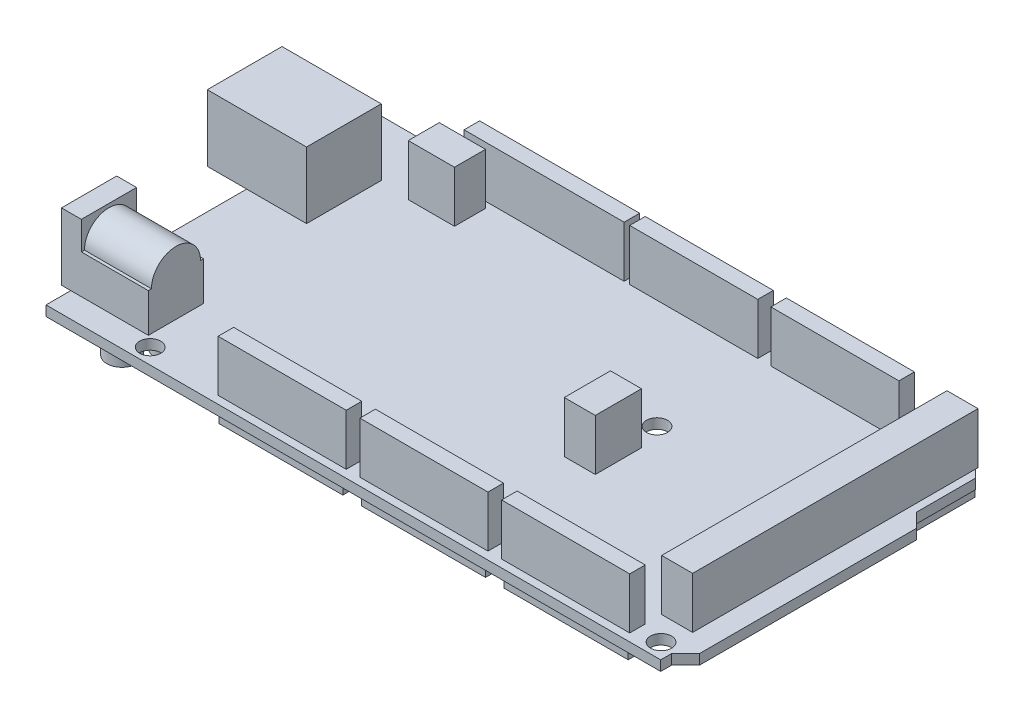
SolidWorks part; units mm, degrees
ref_plane "Front Plane" through (0, 0, 0) normal (0, 0, 1) x (1, 0, 0)
ref_plane "Top Plane" through (0, 0, 0) normal (0, 1, 0) x (1, 0, 0)
ref_plane "Right Plane" through (0, 0, 0) normal (1, 0, 0) x (0, 0, -1)
sketch "Sketch2" plane through (0, 0, 0) normal (0, 1, 0) x (1, 0, 0)
  line L0 (99.1, 0) -> (99.1, 1.75)
  line L2 (0, 0) -> (0, 53.4)
  line L3 (0, 53.4) -> (96.45, 53.4)
  line L4 (101.35, 4) -> (101.35, 39)
  line L5 (0, 0) -> (101.35, 53.4) construction
  line L6 (0, 53.4) -> (101.35, 0) construction
  line L7 (99.1, 1.75) -> (101.35, 4)
  line L8 (0, 0) -> (99.1, 0)
  line L9 (99.1, 0) -> (101.35, 0) construction
  line L10 (101.35, 0) -> (101.35, 4) construction
  line L11 (101.35, 39) -> (99.1, 41.25)
  line L12 (99.1, 41.25) -> (99.1, 50.75)
  line L13 (99.1, 50.75) -> (96.45, 53.4)
  line L14 (96.45, 53.4) -> (101.35, 53.4) construction
  line L15 (101.35, 53.4) -> (101.35, 39) construction
  circle A0 centre (96.65, 2.5) radius 1.7
  circle A1 centre (90.65, 50.95) radius 1.7
  circle A2 centre (15.45, 50.95) radius 1.7
  circle A3 centre (14.3, 2.5) radius 1.7
  circle A4 centre (66.2, 32.3) radius 1.7
  circle A5 centre (66.2, 7.7) radius 1.7
  point P4 (50.675, 26.7)
  point P25 (90.65, 52.65)
  point P26 (92.35, 50.95)
  point P27 (13.75, 50.95)
  point P28 (12.6, 2.5)
  point P29 (14.3, 0.8)
  point P30 (96.65, 0.8)
  point P31 (98.35, 2.5)
  point P32 (66.2, 6)
  point P33 (66.2, 9.4)
  point P34 (66.2, 30.6)
  point P35 (66.2, 34)
  point P36 (67.9, 32.3)
  point P37 (64.5, 32.3)
  point P38 (64.5, 7.7)
  point P39 (67.9, 7.7)
  point P46 (99.1, 46)
  dimension "D9" = 3.4
  dimension "D1" = 101.35
  dimension "D2" = 53.4
  dimension "D3" = 45
  dimension "D4" = 4
  dimension "D5" = 2.25
  dimension "D6" = 35
  dimension "D7" = 9.5
  dimension "D8" = 45
  dimension "D10" = 0.75
  dimension "D11" = 0.8
  dimension "D12" = 6
  dimension "D13" = 24.6
  dimension "D14" = 12.6
  dimension "D15" = 13.75
  dimension "D16" = 3
  dimension "D17" = 6.75
  dimension "D18" = 64.5
extrude "Boss-Extrude1" add sketch "Sketch2" along normal blind 1.625 contours L2 L3 L13 L12 L11 L4 L7 L0 L8
sketch "Sketch3" plane through (0, 1.625, 0) normal (0, 1, 0) x (1, 0, 0)
  line L0 (96.45, 53.4) -> (0, 53.4) construction
  line L1 (-6.35, 44.4) -> (9.65, 44.4)
  line L2 (-6.35, 44.4) -> (-6.35, 32.35)
  line L3 (-6.35, 32.35) -> (9.65, 32.35)
  line L4 (9.65, 44.4) -> (9.65, 32.35)
  line L5 (-6.35, 44.4) -> (9.65, 32.35) construction
  line L6 (-6.35, 32.35) -> (9.65, 44.4) construction
  line L7 (0, 53.4) -> (0, 0) construction
  point P4 (1.65, 38.375)
  dimension "D1" = 12.05
  dimension "D2" = 16
  dimension "D3" = 9
  dimension "D4" = 6.35
extrude "Boss-Extrude2" add sketch "Sketch3" along normal blind 10.7
sketch "Sketch4" plane through (0, 1.625, 0) normal (0, 1, 0) x (1, 0, 0)
  line L0 (0, 32.35) -> (0, 0) construction
  line L1 (-1.5, 12.9) -> (12.5, 12.9)
  line L2 (-1.5, 12.9) -> (-1.5, 4)
  line L3 (-1.5, 4) -> (12.5, 4)
  line L4 (12.5, 12.9) -> (12.5, 4)
  line L5 (-1.5, 12.9) -> (12.5, 4) construction
  line L6 (-1.5, 4) -> (12.5, 12.9) construction
  line L7 (0, 0) -> (99.1, 0) construction
  point P4 (5.5, 8.45)
  dimension "D1" = 1.5
  dimension "D2" = 4
  dimension "D3" = 8.9
  dimension "D4" = 14
extrude "Boss-Extrude3" add sketch "Sketch4" along normal blind 6.25
sketch "Sketch5" plane through (0, 7.875, 0) normal (0, 1, 0) x (1, 0, 0)
  line L0 (-1.5, 4) -> (12.5, 4) construction
  line L1 (-1.5, 12.9) -> (1.7, 12.9)
  line L2 (-1.5, 12.9) -> (-1.5, 4)
  line L3 (-1.5, 4) -> (1.7, 4)
  line L4 (1.7, 12.9) -> (1.7, 4)
  line L5 (-1.5, 12.9) -> (1.7, 4) construction
  line L6 (-1.5, 4) -> (1.7, 12.9) construction
  point P4 (0.1, 8.45)
  dimension "D1" = 3.2
extrude "Boss-Extrude4" add sketch "Sketch5" along normal blind 4.55 contours L2 L3 L4 L1
sketch "Sketch6" plane through (1.7, 0, 0) normal (1, 0, 0) x (0, 0, -1)
  line L0 (12.9, 7.875) -> (4, 7.875) construction
  circle A0 centre (8.45, 7.875) radius 3.95
  dimension "D1" = 7.9
extrude "Boss-Extrude5" add sketch "Sketch6" along normal up to surface (10.8 mm away) up to face at (12.5, 4.75, -8.45)
sketch "Sketch7" plane through (0, 0, 0) normal (0, -1, 0) x (1, 0, 0)
  line L0 (0, -53.4) -> (0, 0) construction
  line L1 (0, 0) -> (99.1, 0) construction
  line L2 (96.45, -53.4) -> (0, -53.4) construction
  line L3 (101.35, -4) -> (101.35, -39) construction
  line L4 (93.1, -7.15) -> (97.6, -7.15)
  line L5 (93.1, -7.15) -> (93.1, -52.15)
  line L6 (93.1, -52.15) -> (97.6, -52.15)
  line L7 (97.6, -7.15) -> (97.6, -52.15)
  line L8 (93.1, -7.15) -> (97.6, -52.15) construction
  line L9 (93.1, -52.15) -> (97.6, -7.15) construction
  line L10 (87.6, -52.4) -> (67.6, -52.4)
  line L11 (87.6, -52.4) -> (87.6, -49.65)
  line L12 (87.6, -49.65) -> (67.6, -49.65)
  line L13 (67.6, -52.4) -> (67.6, -49.65)
  line L14 (87.6, -52.4) -> (67.6, -49.65) construction
  line L15 (87.6, -49.65) -> (67.6, -52.4) construction
  line L16 (64.6, -52.4) -> (44.6, -52.4)
  line L17 (64.6, -52.4) -> (64.6, -49.65)
  line L18 (64.6, -49.65) -> (44.6, -49.65)
  line L19 (44.6, -52.4) -> (44.6, -49.65)
  line L20 (64.6, -52.4) -> (44.6, -49.65) construction
  line L21 (64.6, -49.65) -> (44.6, -52.4) construction
  line L22 (42.6, -52.4) -> (18.1, -52.4)
  line L23 (42.6, -52.4) -> (42.6, -49.65)
  line L24 (42.6, -49.65) -> (18.1, -49.65)
  line L25 (18.1, -52.4) -> (18.1, -49.65)
  line L26 (42.6, -52.4) -> (18.1, -49.65) construction
  line L27 (42.6, -49.65) -> (18.1, -52.4) construction
  line L28 (92.35, -4.25) -> (72.35, -4.25)
  line L29 (92.35, -4.25) -> (92.35, -1.5)
  line L30 (92.35, -1.5) -> (72.35, -1.5)
  line L31 (72.35, -4.25) -> (72.35, -1.5)
  line L32 (92.35, -4.25) -> (72.35, -1.5) construction
  line L33 (92.35, -1.5) -> (72.35, -4.25) construction
  line L34 (69.35, -4.25) -> (49.35, -4.25)
  line L35 (69.35, -4.25) -> (69.35, -1.5)
  line L36 (69.35, -1.5) -> (49.35, -1.5)
  line L37 (49.35, -4.25) -> (49.35, -1.5)
  line L38 (69.35, -4.25) -> (49.35, -1.5) construction
  line L39 (69.35, -1.5) -> (49.35, -4.25) construction
  line L40 (46.35, -4.25) -> (26.35, -4.25)
  line L41 (46.35, -4.25) -> (46.35, -1.5)
  line L42 (46.35, -1.5) -> (26.35, -1.5)
  line L43 (26.35, -4.25) -> (26.35, -1.5)
  line L44 (46.35, -4.25) -> (26.35, -1.5) construction
  line L45 (46.35, -1.5) -> (26.35, -4.25) construction
  line L47 (66.2, -28.3) -> (61.95, -28.3)
  line L48 (66.2, -28.3) -> (66.2, -21.3)
  line L49 (66.2, -21.3) -> (61.95, -21.3)
  line L50 (61.95, -28.3) -> (61.95, -21.3)
  line L51 (66.2, -28.3) -> (61.95, -21.3) construction
  line L52 (66.2, -21.3) -> (61.95, -28.3) construction
  circle A0 centre (9, -3.25) radius 2.43
  circle A1 centre (6, -8) radius 2.43
  circle A2 centre (12, -8) radius 2.43
  circle A3 centre (4, -32.65) radius 1.75
  circle A4 centre (4, -44.65) radius 1.75
  circle A6 centre (66.2, -32.3) radius 1.7 construction
  circle A7 centre (66.2, -32.3) radius 1.7 construction
  point P20 (95.35, -29.65)
  point P25 (77.6, -51.025)
  point P30 (54.6, -51.025)
  point P35 (30.35, -51.025)
  point P40 (82.35, -2.875)
  point P45 (59.35, -2.875)
  point P50 (36.35, -2.875)
  point P51 (49.35, -2.875)
  point P63 (64.075, -24.8)
  dimension "D1" = 4.86
  dimension "D7" = 3.5
  dimension "D25" = 1
  dimension "D27" = 4
  dimension "D30" = 5.5
  dimension "D2" = 9
  dimension "D3" = 3.25
  dimension "D4" = 4.75
  dimension "D5" = 3
  dimension "D6" = 3
  dimension "D8" = 4
  dimension "D9" = 12
  dimension "D10" = 8.75
  dimension "D11" = 2.75
  dimension "D12" = 4.5
  dimension "D13" = 24.5
  dimension "D14" = 20
  dimension "D15" = 20
  dimension "D16" = 45
  dimension "D17" = 20
  dimension "D18" = 20
  dimension "D19" = 20
  dimension "D20" = 3.75
  dimension "D21" = 1.25
  dimension "D22" = 9
  dimension "D23" = 3
  dimension "D24" = 3
  dimension "D26" = 1.5
  dimension "D28" = 7
  dimension "D29" = 4.25
  dimension "D31" = 3
  dimension "D32" = 2
extrude "Boss-Extrude6" add sketch "Sketch7" along normal blind 2.5 contours L7 L6 L5 L4
sketch "Sketch8" plane through (0, 1.625, 0) normal (0, 1, 0) x (1, 0, 0)
  line L0 (96.45, 53.4) -> (0, 53.4) construction
  line L1 (17.5, 52.4) -> (43.3, 52.4)
  line L2 (17.5, 52.4) -> (17.5, 49.9)
  line L3 (17.5, 49.9) -> (43.3, 49.9)
  line L4 (43.3, 52.4) -> (43.3, 49.9)
  line L5 (17.5, 52.4) -> (43.3, 49.9) construction
  line L6 (17.5, 49.9) -> (43.3, 52.4) construction
  line L7 (44.2, 52.4) -> (64.85, 52.4)
  line L8 (44.2, 52.4) -> (44.2, 49.9)
  line L9 (44.2, 49.9) -> (64.85, 49.9)
  line L10 (64.85, 52.4) -> (64.85, 49.9)
  line L11 (44.2, 52.4) -> (64.85, 49.9) construction
  line L12 (44.2, 49.9) -> (64.85, 52.4) construction
  line L13 (66.95, 52.4) -> (87.6, 52.4)
  line L14 (66.95, 52.4) -> (66.95, 49.9)
  line L15 (66.95, 49.9) -> (87.6, 49.9)
  line L16 (87.6, 52.4) -> (87.6, 49.9)
  line L17 (66.95, 52.4) -> (87.6, 49.9) construction
  line L18 (66.95, 49.9) -> (87.6, 52.4) construction
  line L19 (92.85, 52.4) -> (97.85, 52.4)
  line L20 (92.85, 52.4) -> (92.85, 6.4)
  line L21 (92.85, 6.4) -> (97.85, 6.4)
  line L22 (97.85, 52.4) -> (97.85, 6.4)
  line L23 (92.85, 52.4) -> (97.85, 6.4) construction
  line L24 (92.85, 6.4) -> (97.85, 52.4) construction
  line L25 (26.5, 1.25) -> (47.15, 1.25)
  line L26 (26.5, 1.25) -> (26.5, 3.75)
  line L27 (26.5, 3.75) -> (47.15, 3.75)
  line L28 (47.15, 1.25) -> (47.15, 3.75)
  line L29 (26.5, 1.25) -> (47.15, 3.75) construction
  line L30 (26.5, 3.75) -> (47.15, 1.25) construction
  line L31 (49.35, 1.25) -> (70, 1.25)
  line L32 (49.35, 1.25) -> (49.35, 3.75)
  line L33 (49.35, 3.75) -> (70, 3.75)
  line L34 (70, 1.25) -> (70, 3.75)
  line L35 (49.35, 1.25) -> (70, 3.75) construction
  line L36 (49.35, 3.75) -> (70, 1.25) construction
  line L37 (72.2, 1.25) -> (92.85, 1.25)
  line L38 (72.2, 1.25) -> (72.2, 3.75)
  line L39 (72.2, 3.75) -> (92.85, 3.75)
  line L40 (92.85, 1.25) -> (92.85, 3.75)
  line L41 (72.2, 1.25) -> (92.85, 3.75) construction
  line L42 (72.2, 3.75) -> (92.85, 1.25) construction
  line L43 (62.95, 28.05) -> (67.95, 28.05)
  line L44 (62.95, 28.05) -> (62.95, 20.6)
  line L45 (62.95, 20.6) -> (67.95, 20.6)
  line L46 (67.95, 28.05) -> (67.95, 20.6)
  line L47 (62.95, 28.05) -> (67.95, 20.6) construction
  line L48 (62.95, 20.6) -> (67.95, 28.05) construction
  line L49 (14.5, 48.9) -> (21.95, 48.9)
  line L50 (14.5, 48.9) -> (14.5, 43.9)
  line L51 (14.5, 43.9) -> (21.95, 43.9)
  line L52 (21.95, 48.9) -> (21.95, 43.9)
  line L53 (14.5, 48.9) -> (21.95, 43.9) construction
  line L54 (14.5, 43.9) -> (21.95, 48.9) construction
  line L55 (0, 53.4) -> (0, 44.4) construction
  line L56 (0, 0) -> (99.1, 0) construction
  line L57 (101.35, 4) -> (101.35, 39) construction
  circle A0 centre (15.45, 50.95) radius 1.7 construction
  circle A1 centre (15.45, 50.95) radius 1.7 construction
  circle A3 centre (66.2, 32.3) radius 1.7 construction
  point P4 (30.4, 51.15)
  point P9 (54.525, 51.15)
  point P14 (77.275, 51.15)
  point P19 (95.35, 29.4)
  point P24 (36.825, 2.5)
  point P29 (59.675, 2.5)
  point P34 (82.525, 2.5)
  point P39 (65.45, 24.325)
  point P44 (18.225, 46.4)
  point P51 (44.2, 51.15)
  point P53 (64.85, 51.15)
  point P57 (13.75, 50.95)
  point P60 (49.35, 2.5)
  point P61 (72.2, 2.5)
  dimension "D22" = 4.25
  dimension "D1" = 5
  dimension "D2" = 2.5
  dimension "D3" = 7.45
  dimension "D4" = 7.45
  dimension "D5" = 46
  dimension "D6" = 25.8
  dimension "D7" = 20.65
  dimension "D8" = 20.65
  dimension "D9" = 1
  dimension "D10" = 0.9
  dimension "D11" = 2.1
  dimension "D12" = 3.75
  dimension "D13" = 1
  dimension "D14" = 14.5
  dimension "D15" = 1.25
  dimension "D16" = 20.65
  dimension "D17" = 20.65
  dimension "D18" = 20.65
  dimension "D19" = 2.2
  dimension "D20" = 2.2
  dimension "D21" = 8.5
  dimension "D23" = 3.25
  dimension "D24" = 3.5
  dimension "D25" = 1
extrude "Boss-Extrude7" add sketch "Sketch8" along normal blind 8.25 contours L25 L28 L27 L26
